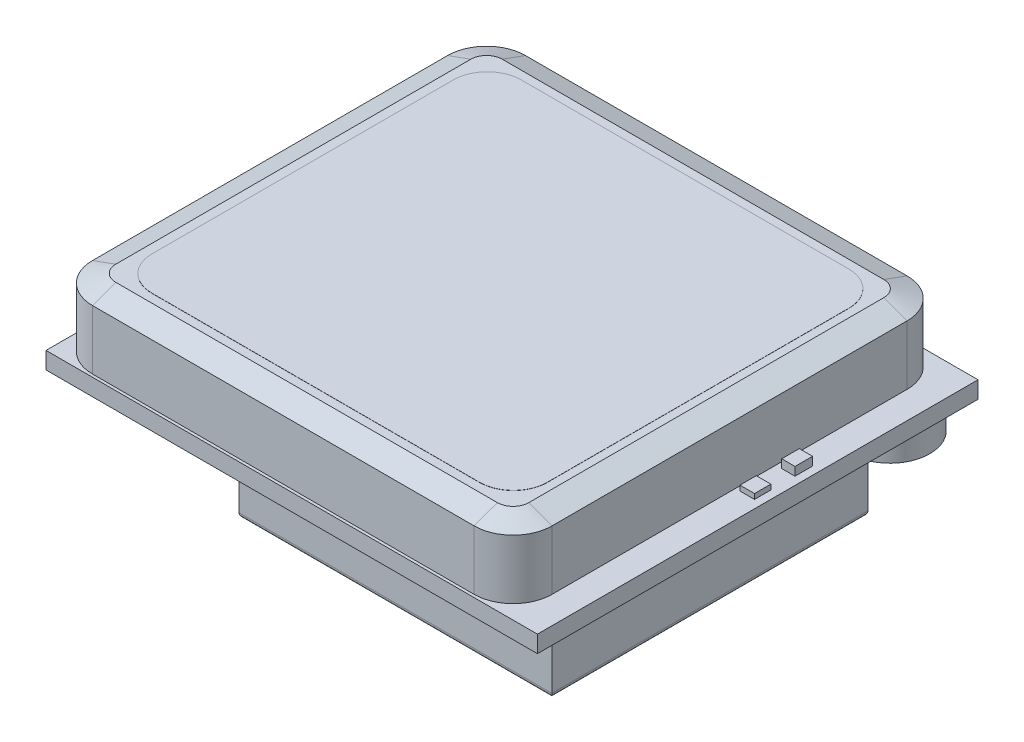
SolidWorks part; units mm, degrees
ref_plane "前视基准面" through (0, 0, 0) normal (0, 0, 1) x (1, 0, 0)
ref_plane "上视基准面" through (0, 0, 0) normal (0, 1, 0) x (1, 0, 0)
ref_plane "右视基准面" through (0, 0, 0) normal (1, 0, 0) x (0, 0, -1)
sketch "草图2" plane through (0, 0, 0) normal (0, 1, 0) x (1, 0, 0)
  line L0 (0, 0) -> (0, 26)
  line L1 (0, 26) -> (29, 26)
  line L2 (29, 26) -> (29, 0)
  line L3 (29, 0) -> (0, 0)
extrude "凸台-拉伸1" add sketch "草图2" along normal blind 1
sketch "草图3" plane through (0, 1, 0) normal (0, 1, 0) x (1, 0, 0)
  line L1 (25.0985, 25.7177) -> (2.5792, 25.7177)
  line L2 (27.3985, 23.4177) -> (27.3985, 2.4647)
  line L3 (25.0985, 0.1647) -> (2.5792, 0.1647)
  line L4 (0.2792, 23.4177) -> (0.2792, 2.4647)
  arc A0 (25.0985, 0.1647) -> (27.3985, 2.4647) centre (25.0985, 2.4647) ccw
  arc A1 (27.3985, 23.4177) -> (25.0985, 25.7177) centre (25.0985, 23.4177) ccw
  arc A2 (2.5792, 25.7177) -> (0.2792, 23.4177) centre (2.5792, 23.4177) ccw
  arc A3 (2.5792, 0.1647) -> (0.2792, 2.4647) centre (2.5792, 2.4647) cw
extrude "凸台-拉伸2" add sketch "草图3" along normal blind 4
sketch "草图4" plane through (0, 5, 0) normal (0, 1, 0) x (1, 0, 0)
  line L1 (4.2042, 23.8372) -> (23.5421, 23.8372)
  line L2 (2.2042, 21.8372) -> (2.2042, 4.0423)
  line L3 (4.2042, 2.0423) -> (23.5421, 2.0423)
  line L4 (25.5421, 21.8372) -> (25.5421, 4.0423)
  arc A0 (4.2042, 2.0423) -> (2.2042, 4.0423) centre (4.2042, 4.0423) cw
  arc A1 (23.5421, 2.0423) -> (25.5421, 4.0423) centre (23.5421, 4.0423) ccw
  arc A2 (25.5421, 21.8372) -> (23.5421, 23.8372) centre (23.5421, 21.8372) ccw
  arc A3 (4.2042, 23.8372) -> (2.2042, 21.8372) centre (4.2042, 21.8372) ccw
  dimension "D1" = 2
extrude "凸台-拉伸3" add sketch "草图4" along normal blind 0.01
sketch "草图5" plane through (0, 1, 0) normal (0, 1, 0) x (1, 0, 0)
  line L1 (27.7454, 16.7071) -> (28.5296, 16.7071)
  line L2 (27.7454, 16.7071) -> (27.7454, 15.6705)
  line L3 (27.7454, 15.6705) -> (28.5296, 15.6705)
  line L4 (28.5296, 16.7071) -> (28.5296, 15.6705)
extrude "凸台-拉伸4" add sketch "草图5" along normal blind 0.5
sketch "草图6" plane through (0, 1, 0) normal (0, 1, 0) x (1, 0, 0)
  line L1 (27.6607, 14.2546) -> (28.5215, 14.2546)
  line L2 (27.6607, 14.2546) -> (27.6607, 13.2898)
  line L3 (27.6607, 13.2898) -> (28.5215, 13.2898)
  line L4 (28.5215, 14.2546) -> (28.5215, 13.2898)
extrude "凸台-拉伸5" add sketch "草图6" along normal blind 0.3
sketch "草图7" plane through (0, 0, 0) normal (0, -1, 0) x (1, 0, 0)
  line L1 (10.2809, -1.102) -> (28.7487, -1.102)
  line L2 (10.2809, -1.102) -> (10.2809, -19.7627)
  line L3 (10.2809, -19.7627) -> (28.7487, -19.7627)
  line L4 (28.7487, -1.102) -> (28.7487, -19.7627)
extrude "凸台-拉伸6" add sketch "草图7" along normal blind 3
fillet "圆角1" radius 0.3 4 edges at (19.5148, -3, -1.102) (28.7487, -3, -10.4323) (19.5148, -3, -19.7627) (10.2809, -3, -10.4323)
sketch "草图8" plane through (0, 0, 0) normal (0, -1, 0) x (1, 0, 0)
  circle A0 centre (26.5137, -23.2944) radius 2.3474
extrude "凸台-拉伸7" add sketch "草图8" along normal blind 1.5
sketch "草图9" plane through (0, 0, 0) normal (0, -1, 0) x (1, 0, 0)
  line L1 (1.3315, -2.1477) -> (4.2164, -2.1477)
  line L2 (1.3315, -2.1477) -> (1.3315, -3.4482)
  line L3 (1.3315, -3.4482) -> (4.2164, -3.4482)
  line L4 (4.2164, -2.1477) -> (4.2164, -3.4482)
  line L5 (3.7391, -21.5338) -> (6.8367, -21.5338)
  line L6 (3.7391, -21.5338) -> (3.7391, -24.6584)
  line L7 (3.7391, -24.6584) -> (6.8367, -24.6584)
  line L8 (6.8367, -21.5338) -> (6.8367, -24.6584)
  line L9 (14.7139, -24.3742) -> (16.3209, -24.3742)
  line L10 (14.7139, -24.3742) -> (14.7139, -25.4333)
  line L11 (14.7139, -25.4333) -> (16.3209, -25.4333)
  line L12 (16.3209, -24.3742) -> (16.3209, -25.4333)
  line L13 (17.4457, -23.242) -> (20.236, -23.242)
  line L14 (17.4457, -23.242) -> (17.4457, -24.5276)
  line L15 (17.4457, -24.5276) -> (20.236, -24.5276)
  line L16 (20.236, -23.242) -> (20.236, -24.5276)
extrude "凸台-拉伸8" add sketch "草图9" along normal blind 0.5
sketch "草图10" plane through (0, 0, 0) normal (0, -1, 0) x (1, 0, 0)
  line L1 (0.8316, -20.256) -> (2.3886, -20.256)
  line L2 (0.8316, -20.256) -> (0.8316, -22.3168)
  line L3 (0.8316, -22.3168) -> (2.3886, -22.3168)
  line L4 (2.3886, -20.256) -> (2.3886, -22.3168)
extrude "凸台-拉伸9" add sketch "草图10" along normal blind 0.8
sketch "草图11" plane through (0, 0, 0) normal (0, -1, 0) x (1, 0, 0)
  line L1 (5.2185, -1.7461) -> (5.8453, -1.7461)
  line L2 (5.2185, -1.7461) -> (5.2185, -2.3159)
  line L3 (5.2185, -2.3159) -> (5.8453, -2.3159)
  line L4 (5.8453, -1.7461) -> (5.8453, -2.3159)
  line L5 (5.7313, -3.8543) -> (6.3391, -3.8543)
  line L6 (5.7313, -3.8543) -> (5.7313, -4.5191)
  line L7 (5.7313, -4.5191) -> (6.3391, -4.5191)
  line L8 (6.3391, -3.8543) -> (6.3391, -4.5191)
  line L9 (6.9944, -3.8543) -> (7.5262, -3.8543)
  line L10 (6.9944, -3.8543) -> (6.9944, -4.5191)
  line L11 (6.9944, -4.5191) -> (7.5262, -4.5191)
  line L12 (7.5262, -3.8543) -> (7.5262, -4.5191)
  line L13 (8.134, -3.8543) -> (8.6658, -3.8543)
  line L14 (8.134, -3.8543) -> (8.134, -4.4526)
  line L15 (8.134, -4.4526) -> (8.6658, -4.4526)
  line L16 (8.6658, -3.8543) -> (8.6658, -4.4526)
  line L17 (6.9944, -6.314) -> (7.5262, -6.314)
  line L18 (6.9944, -6.314) -> (6.9944, -6.9408)
  line L19 (6.9944, -6.9408) -> (7.5262, -6.9408)
  line L20 (7.5262, -6.314) -> (7.5262, -6.9408)
  line L21 (8.134, -6.314) -> (8.6658, -6.314)
  line L22 (8.134, -6.314) -> (8.134, -6.9408)
  line L23 (8.134, -6.9408) -> (8.6658, -6.9408)
  line L24 (8.6658, -6.314) -> (8.6658, -6.9408)
  line L25 (8.134, -12.824) -> (8.6658, -12.824)
  line L26 (8.134, -12.824) -> (8.134, -13.3912)
  line L27 (8.134, -13.3912) -> (8.6658, -13.3912)
  line L28 (8.6658, -12.824) -> (8.6658, -13.3912)
  line L29 (8.134, -14.9087) -> (8.6658, -14.9087)
  line L30 (8.134, -14.9087) -> (8.134, -15.5372)
  line L31 (8.134, -15.5372) -> (8.6658, -15.5372)
  line L32 (8.6658, -14.9087) -> (8.6658, -15.5372)
  line L33 (8.134, -17.116) -> (8.6658, -17.116)
  line L34 (8.134, -17.116) -> (8.134, -17.7292)
  line L35 (8.134, -17.7292) -> (8.6658, -17.7292)
  line L36 (8.6658, -17.116) -> (8.6658, -17.7292)
  line L37 (6.4859, -17.0624) -> (6.9228, -17.0624)
  line L38 (6.4859, -17.0624) -> (6.4859, -17.5989)
  line L39 (6.4859, -17.5989) -> (6.9228, -17.5989)
  line L40 (6.9228, -17.0624) -> (6.9228, -17.5989)
  line L41 (12.2322, -24.6329) -> (12.9056, -24.6329)
  line L42 (12.2322, -24.6329) -> (12.2322, -25.2629)
  line L43 (12.2322, -25.2629) -> (12.9056, -25.2629)
  line L44 (12.9056, -24.6329) -> (12.9056, -25.2629)
  line L45 (21.3012, -22.5911) -> (21.9203, -22.5911)
  line L46 (21.3012, -22.5911) -> (21.3012, -23.2645)
  line L47 (21.3012, -23.2645) -> (21.9203, -23.2645)
  line L48 (21.9203, -22.5911) -> (21.9203, -23.2645)
  line L49 (1.4861, -24.6329) -> (2.1274, -24.6329)
  line L50 (1.4861, -24.6329) -> (1.4861, -25.2629)
  line L51 (1.4861, -25.2629) -> (2.1274, -25.2629)
  line L52 (2.1274, -24.6329) -> (2.1274, -25.2629)
  line L53 (7.9312, -22.3734) -> (8.3999, -22.3734)
  line L54 (7.9312, -22.3734) -> (7.9312, -22.9278)
  line L55 (7.9312, -22.9278) -> (8.3999, -22.9278)
  line L56 (8.3999, -22.3734) -> (8.3999, -22.9278)
extrude "凸台-拉伸10" add sketch "草图11" along normal blind 0.4
sketch "草图12" plane through (0, 0, 0) normal (0, -1, 0) x (1, 0, 0)
  line L0 (1.0329, -7.2447) -> (2.7013, -7.2447)
  line L1 (2.7013, -7.2447) -> (2.7013, -5.7404)
  line L2 (2.7013, -5.7404) -> (4.862, -5.7404)
  line L3 (4.862, -5.7404) -> (5.4501, -6.2874)
  line L4 (5.4501, -6.2874) -> (5.4501, -7.2447)
  line L5 (5.4501, -7.2447) -> (5.8193, -7.2447)
  line L6 (5.8193, -7.2447) -> (5.8193, -8.6942)
  line L7 (5.8193, -8.6942) -> (5.4501, -8.6942)
  line L8 (5.4501, -8.6942) -> (5.4501, -9.1045)
  line L9 (5.4501, -9.1045) -> (5.8193, -9.1045)
  line L10 (5.8193, -9.1045) -> (5.8193, -10.0344)
  line L11 (5.8193, -10.0344) -> (5.4501, -10.0344)
  line L12 (5.4501, -10.0344) -> (5.4501, -10.4037)
  line L13 (5.4501, -10.4037) -> (5.8193, -10.4037)
  line L14 (5.8193, -10.4037) -> (5.8193, -11.3883)
  line L15 (5.8193, -11.3883) -> (5.4501, -11.3883)
  line L16 (5.4501, -11.3883) -> (5.4501, -11.7575)
  line L17 (5.4501, -11.7575) -> (5.8193, -11.7575)
  line L18 (5.8193, -11.7575) -> (5.8193, -12.7148)
  line L19 (5.8193, -12.7148) -> (5.4501, -12.7148)
  line L20 (5.4501, -12.7148) -> (5.4501, -13.0293)
  line L21 (5.4501, -13.0293) -> (5.8193, -13.0293)
  line L22 (5.8193, -13.0293) -> (5.8193, -14.0823)
  line L23 (5.8193, -14.0823) -> (5.5458, -14.0823)
  line L24 (5.5458, -14.0823) -> (5.5458, -14.3285)
  line L25 (5.5458, -14.3285) -> (5.8193, -14.3285)
  line L26 (5.8193, -14.3285) -> (5.8193, -15.3952)
  line L27 (5.8193, -15.3952) -> (5.5458, -15.3952)
  line L28 (5.5458, -15.3952) -> (5.5458, -15.7371)
  line L29 (5.5458, -15.7371) -> (5.8193, -15.7371)
  line L30 (5.8193, -15.7371) -> (5.8193, -17.3371)
  line L31 (5.8193, -17.3371) -> (5.4501, -17.3371)
  line L32 (5.4501, -17.3371) -> (5.4501, -18.1439)
  line L33 (5.4501, -18.1439) -> (4.7763, -18.8682)
  line L34 (4.7763, -18.8682) -> (2.7013, -18.8682)
  line L35 (2.7013, -18.8682) -> (2.7013, -17.4191)
  line L36 (2.7013, -17.4191) -> (1.0329, -17.4191)
  line L37 (1.0329, -17.4191) -> (1.0329, -7.2447)
extrude "凸台-拉伸11" add sketch "草图12" along normal blind 3
sketch "草图13" plane through (0, -3, 0) normal (0, -1, 0) x (1, 0, 0)
  line L0 (1.6902, -17.4191) -> (5.4501, -17.4191)
  line L1 (1.0329, -17.4191) -> (2.7013, -17.4191) construction
  line L2 (5.4501, -18.1439) -> (5.4501, -17.3371) construction
  line L3 (5.4501, -17.4191) -> (5.4501, -17.3371)
  line L4 (5.4501, -17.3371) -> (5.8193, -17.3371)
  line L5 (5.8193, -17.3371) -> (5.8193, -15.7371)
  line L6 (5.8193, -15.7371) -> (5.5458, -15.7371)
  line L7 (5.5458, -15.7371) -> (5.5458, -15.3952)
  line L8 (5.5458, -15.3952) -> (5.8193, -15.3952)
  line L9 (5.8193, -15.3952) -> (5.8193, -14.3285)
  line L10 (5.8193, -14.3285) -> (5.5458, -14.3285)
  line L11 (5.5458, -14.3285) -> (5.5458, -14.0823)
  line L12 (5.5458, -14.0823) -> (5.8193, -14.0823)
  line L13 (5.8193, -14.0823) -> (5.8193, -13.0293)
  line L14 (5.8193, -13.0293) -> (5.4501, -13.0293)
  line L15 (5.4501, -13.0293) -> (5.4501, -12.7148)
  line L16 (5.4501, -12.7148) -> (5.8193, -12.7148)
  line L17 (5.8193, -12.7148) -> (5.8193, -11.7575)
  line L18 (5.8193, -11.7575) -> (5.4501, -11.7575)
  line L19 (5.4501, -11.7575) -> (5.4501, -11.3883)
  line L20 (5.4501, -11.3883) -> (5.8193, -11.3883)
  line L21 (5.8193, -11.3883) -> (5.8193, -10.4037)
  line L22 (5.8193, -10.4037) -> (5.4501, -10.4037)
  line L23 (5.4501, -10.4037) -> (5.4501, -10.0344)
  line L24 (5.4501, -10.0344) -> (5.8193, -10.0344)
  line L25 (5.8193, -10.0344) -> (5.8193, -9.1045)
  line L26 (5.8193, -9.1045) -> (5.4501, -9.1045)
  line L27 (5.4501, -9.1045) -> (5.4501, -8.6942)
  line L28 (5.4501, -8.6942) -> (5.8193, -8.6942)
  line L29 (5.8193, -8.6942) -> (5.8193, -7.2447)
  line L30 (5.8193, -7.2447) -> (1.6902, -7.2447)
  line L31 (2.7013, -7.2447) -> (1.0329, -7.2447) construction
  line L32 (1.6902, -7.2447) -> (1.6902, -7.7447)
  line L33 (1.6902, -7.7447) -> (2.7013, -7.7447)
  line L34 (1.6902, -17.4191) -> (1.6902, -16.9191)
  line L35 (1.6902, -16.9191) -> (2.7013, -16.9191)
  line L36 (2.7013, -16.9191) -> (2.7013, -7.7447)
extrude "凸台-拉伸12" add sketch "草图13" along normal blind 1
sketch "草图14" plane through (1.0329, 0, 0) normal (-1, 0, 0) x (0, 0, 1)
  line L0 (-17.222, -0.183) -> (-17.222, -2.8175)
  line L1 (-17.222, -2.8175) -> (-16.9212, -2.8175)
  line L2 (-16.9212, -2.8175) -> (-16.9191, -3)
  line L3 (-16.9191, -3) -> (-7.7447, -3)
  line L4 (-7.7447, -3) -> (-7.7447, -2.8175)
  line L5 (-7.7447, -2.8175) -> (-7.4106, -2.8175)
  line L6 (-7.4106, -2.8175) -> (-7.4106, -0.183)
  line L7 (-7.4106, -0.183) -> (-17.222, -0.183)
  circle A0 centre (-11.7271, -2.1277) radius 0.1275
  circle A1 centre (-10.4571, -2.1277) radius 0.1275
  circle A2 centre (-9.1871, -2.1277) radius 0.1275
  circle A3 centre (-12.9971, -2.1277) radius 0.1275
  circle A4 centre (-14.2671, -2.1277) radius 0.1275
  circle A5 centre (-15.5371, -2.1277) radius 0.1275
  dimension "D1" = 3
  dimension "D2" = 4
extrude "切除-拉伸1" cut sketch "草图14" against normal blind 4
chamfer "倒角1" distance 0.5 angle 70 8 edges at (27.3985, 5, -12.9412) (26.7249, 5, -25.0441) (26.7249, 5, -0.8383) (13.8389, 5, -25.7177) (13.8389, 5, -0.1647) (0.9529, 5, -25.0441) (0.9529, 5, -0.8383) (0.2792, 5, -12.9412)
